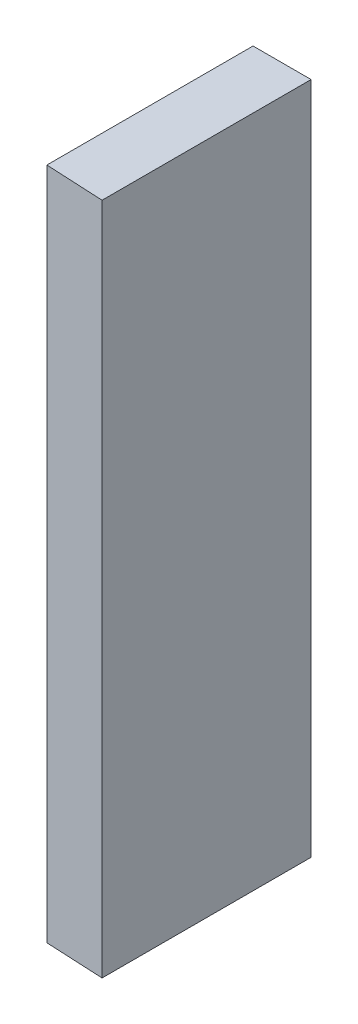
SolidWorks part; units mm, degrees
ref_plane "Plan de face" through (0, 0, 0) normal (0, 0, 1) x (1, 0, 0)
ref_plane "Plan de dessus" through (0, 0, 0) normal (0, 1, 0) x (1, 0, 0)
ref_plane "Plan de droite" through (0, 0, 0) normal (1, 0, 0) x (0, 0, -1)
sketch "Esquisse1" plane through (0, 0, 0) normal (0, 0, 1) x (1, 0, 0)
  line L1 (0, 0) -> (5, 0)
  line L2 (0, 0) -> (0, -58)
  line L3 (0, -58) -> (5, -58)
  line L4 (5, 0) -> (5, -58)
  dimension "D1" = 58
  dimension "D2" = 5
extrude "Boss.-Extru.1" add sketch "Esquisse1" along normal blind 18
sketch "Esquisse2" plane through (0, 0, 0) normal (-1, 0, 0) x (0, 0, 1)
  line L1 (0, -58) -> (3, -58)
  line L2 (0, -58) -> (0, -10.25)
  line L3 (0, -10.25) -> (3, -10.25)
  line L4 (3, -58) -> (3, -10.25)
  dimension "D1" = 47.75
  dimension "D2" = 3
extrude "Boss.-Extru.2" add sketch "Esquisse2" along normal blind 10
sketch "Esquisse3" plane through (0, 0, 3) normal (0, 0, 1) x (1, 0, 0)
  line L0 (-10, -58) -> (0, -58) construction
  circle A0 centre (-5, -15) radius 1.625
  circle A1 centre (-5, -43) radius 1.625
  point P7 (-5, -58)
  dimension "D1" = 3.25
  dimension "D2" = 3.25
  dimension "D3" = 28
  dimension "D4" = 15
extrude "Enlèv. mat.-Extru.1" cut sketch "Esquisse3" against normal through all
sketch "Esquisse4" plane through (0, -58, 0) normal (0, -1, 0) x (1, 0, 0)
  line L0 (0, 18) -> (0, 17.75)
  line L1 (0, 18) -> (0, 3) construction
  line L2 (0, 17.75) -> (5, 18)
  line L3 (5, 18) -> (0, 18)
  dimension "D1" = 0.25
extrude "Enlèv. mat.-Extru.2" cut sketch "Esquisse4" against normal through all
